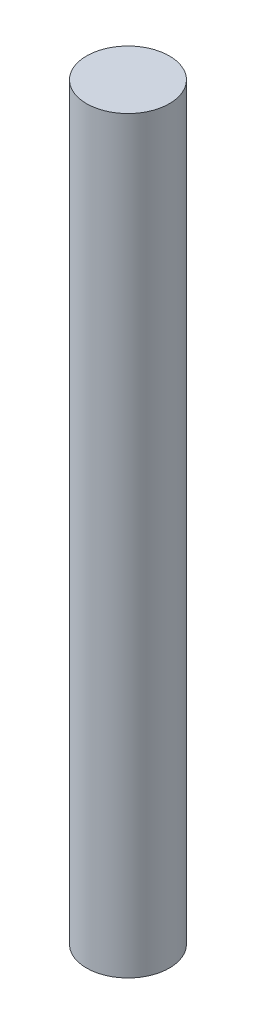
SolidWorks part; units mm, degrees
ref_plane "Front Plane" through (0, 0, 0) normal (0, 0, 1) x (1, 0, 0)
ref_plane "Top Plane" through (0, 0, 0) normal (0, 1, 0) x (1, 0, 0)
ref_plane "Right Plane" through (0, 0, 0) normal (1, 0, 0) x (0, 0, -1)
sketch "Sketch1" plane through (0, 0, 0) normal (0, 1, 0) x (1, 0, 0)
  circle A0 centre (0, 0) radius 7.1875
  dimension "D1" = 14.375
extrude "Boss-Extrude1" add sketch "Sketch1" along normal blind 130
